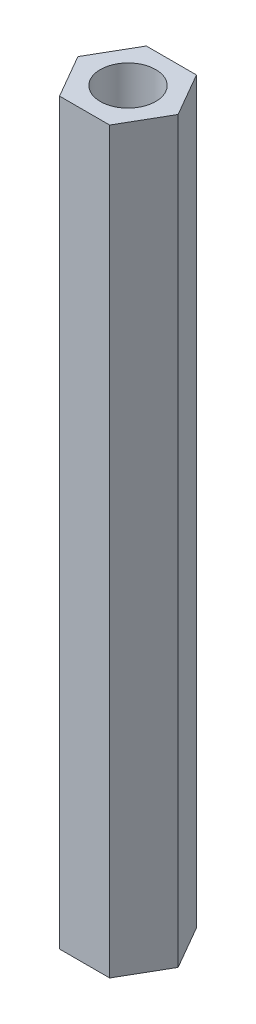
SolidWorks part; units mm, degrees
ref_plane "前视基准面" through (0, 0, 0) normal (0, 0, 1) x (1, 0, 0)
ref_plane "上视基准面" through (0, 0, 0) normal (0, 1, 0) x (1, 0, 0)
ref_plane "右视基准面" through (0, 0, 0) normal (1, 0, 0) x (0, 0, -1)
sketch "草图1" plane through (0, 0, 0) normal (0, 1, 0) x (1, 0, 0)
  line L0 (-1.3568, 2.35) -> (1.3568, 2.35)
  line L1 (1.3568, 2.35) -> (2.7135, 0)
  line L2 (2.7135, 0) -> (1.3568, -2.35)
  line L3 (1.3568, -2.35) -> (-1.3568, -2.35)
  line L4 (-1.3568, -2.35) -> (-2.7135, 0)
  line L5 (-2.7135, 0) -> (-1.3568, 2.35)
  line L6 (-2.7135, 0) -> (2.7135, 0) construction
  line L7 (-1.3568, 2.35) -> (1.3568, -2.35) construction
  circle A0 centre (0, 0) radius 1.5
  point P4 (0, 0)
  dimension "D6" = 3
  dimension "D1" = 4.7
  dimension "D2" = 4.7
  dimension "D3" = 4.7
  dimension "D4" = 120
  dimension "D5" = 120
extrude "凸台-拉伸1" add sketch "草图1" along normal blind 40
